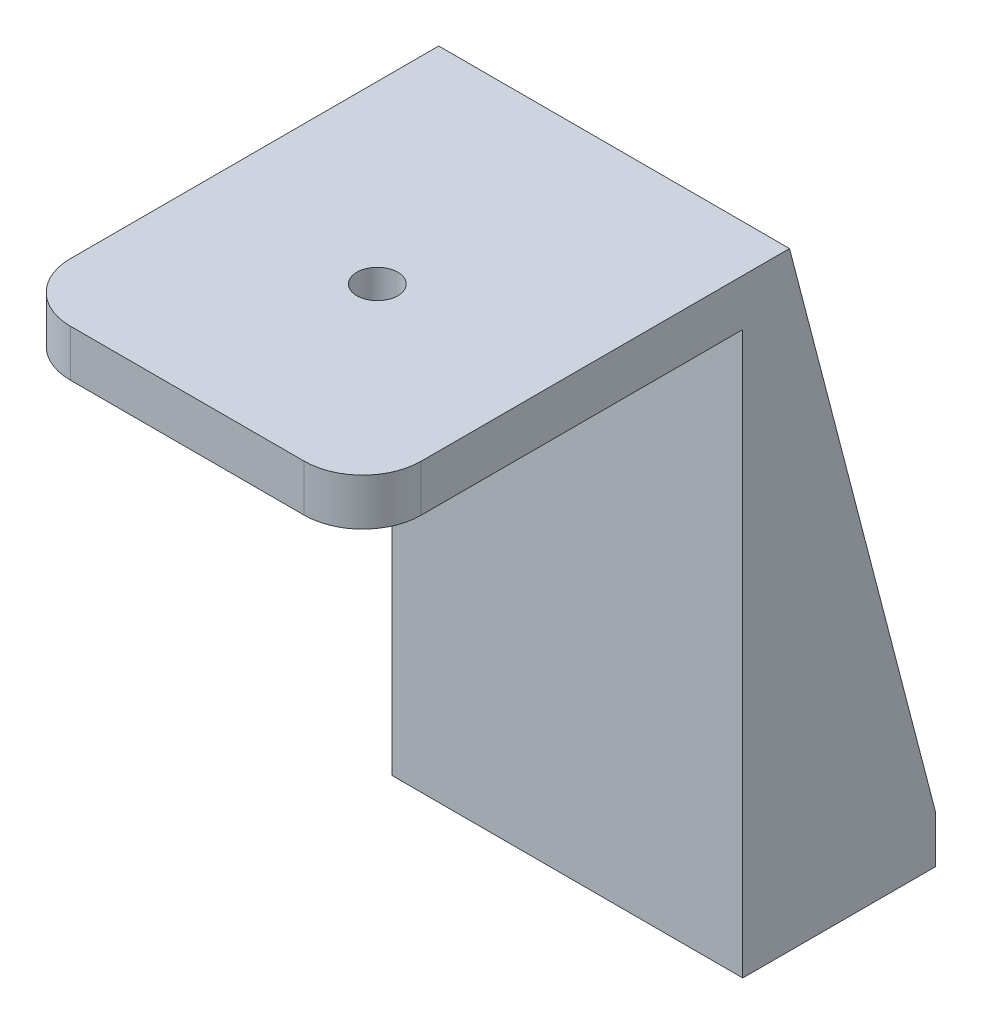
SolidWorks part; units mm, degrees
ref_plane "Front Plane" through (0, 0, 0) normal (0, 0, 1) x (1, 0, 0)
ref_plane "Top Plane" through (0, 0, 0) normal (0, 1, 0) x (1, 0, 0)
ref_plane "Right Plane" through (0, 0, 0) normal (1, 0, 0) x (0, 0, -1)
sketch "Sketch1" plane through (0, 0, 0) normal (0, 1, 0) x (1, 0, 0)
  line L0 (30, -32.5) -> (-30, 32.5) construction
  line L1 (-30, 32.5) -> (30, 32.5)
  line L2 (-30, 32.5) -> (-30, -32.5)
  line L3 (-30, -32.5) -> (30, -32.5)
  line L4 (30, 32.5) -> (30, -32.5)
  dimension "D1" = 60
  dimension "D2" = 65
extrude "Boss-Extrude1" add sketch "Sketch1" along normal blind 8
sketch "Sketch2" plane through (0, 0, 0) normal (0, -1, 0) x (1, 0, 0)
  circle A0 centre (0, 0) radius 19.05
  dimension "D1" = 38.1
extrude "Cut-Extrude1" cut sketch "Sketch2" against normal blind 1.6
sketch "Sketch3" plane through (0, 1.6, 0) normal (0, -1, 0) x (1, 0, 0)
  circle A0 centre (0, 0) radius 3.5
  dimension "D1" = 7
extrude "Cut-Extrude2" cut sketch "Sketch3" against normal through all
sketch "Sketch4" plane through (0, 8, 0) normal (0, 1, 0) x (1, 0, 0)
  line L1 (-30, 32.5) -> (30, 32.5)
  line L2 (-30, 32.5) -> (-30, 40.5)
  line L3 (-30, 40.5) -> (30, 40.5)
  line L4 (30, 32.5) -> (30, 40.5)
  dimension "D1" = 8
extrude "Boss-Extrude2" add sketch "Sketch4" against normal blind 104.05
fillet "Fillet1" radius 10 2 edges at (-30, 4, 32.5) (30, 4, 32.5)
sketch "Sketch5" plane through (0, 0, -40.5) normal (0, 0, -1) x (-1, 0, 0)
  line L0 (30, -96.05) -> (30, 8) construction
  line L1 (-30, -96.05) -> (30, -96.05)
  line L2 (-30, -96.05) -> (-30, -88.05)
  line L3 (-30, -88.05) -> (30, -88.05)
  line L4 (30, -96.05) -> (30, -88.05)
  dimension "D1" = 8
extrude "Boss-Extrude3" add sketch "Sketch5" along normal blind 25
sketch "Sketch6" plane through (30, 0, 0) normal (1, 0, 0) x (0, 0, -1)
  line L0 (40.5, 8) -> (65.5, -88.05)
  line L1 (65.5, -88.05) -> (40.5, -88.05) construction
  line L2 (65.5, -88.05) -> (40.5, -88.05)
  line L3 (40.5, -88.05) -> (40.5, 8) construction
  line L4 (40.5, -88.05) -> (40.5, 8)
extrude "Boss-Extrude4" add sketch "Sketch6" against normal blind 5
mirror "Mirror1" about plane through (0, 0, 0) normal (1, 0, 0) of "Boss-Extrude4"
